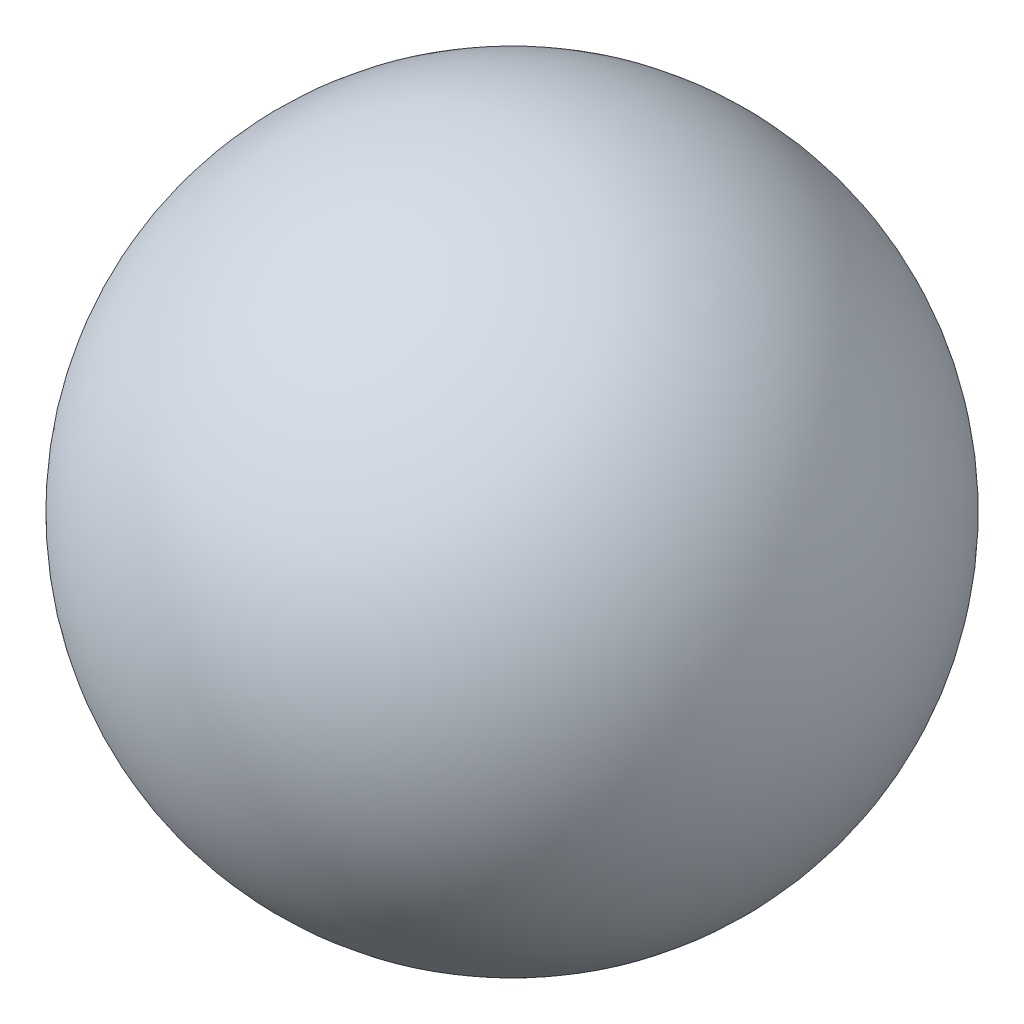
SolidWorks part; units mm, degrees
ref_plane "Front Plane" through (0, 0, 0) normal (0, 0, 1) x (1, 0, 0)
ref_plane "Top Plane" through (0, 0, 0) normal (0, 1, 0) x (1, 0, 0)
ref_plane "Right Plane" through (0, 0, 0) normal (1, 0, 0) x (0, 0, -1)
sketch "Sketch1" plane through (0, 0, 0) normal (0, 0, 1) x (1, 0, 0)
  line L0 (0, 101.8592) -> (0, -101.8592)
  arc A0 (0, 101.8592) -> (0, -101.8592) centre (0, 0) ccw
  dimension "D1" = 203.7183
revolve "Revolve1" add sketch "Sketch1" angle 360 about L0
